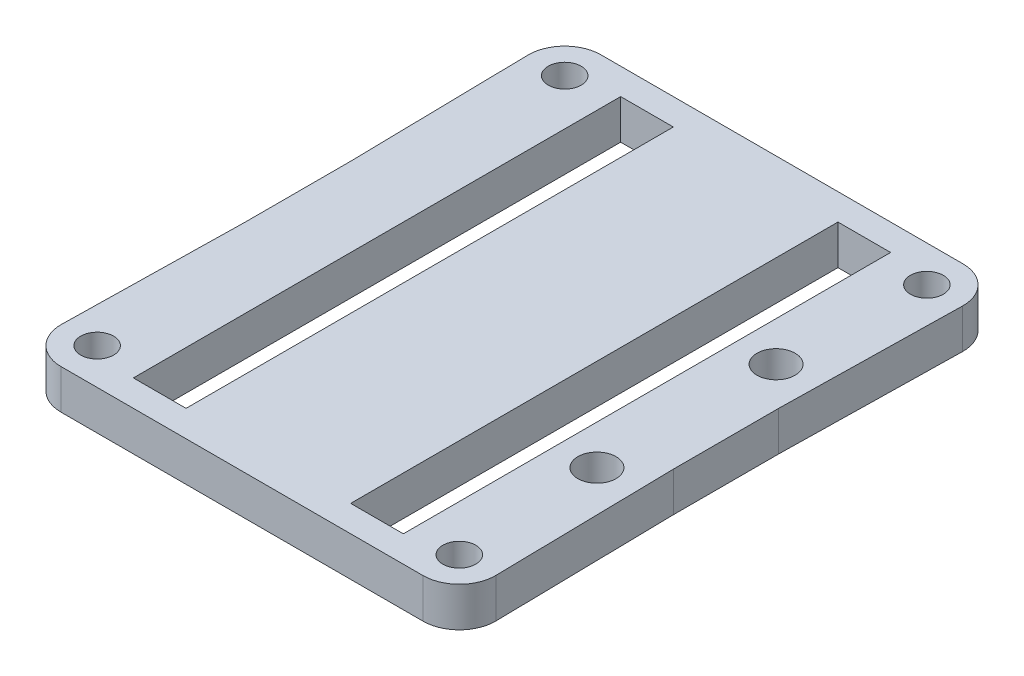
SolidWorks part; units mm, degrees
ref_plane "Front Plane" through (0, 0, 0) normal (0, 0, 1) x (1, 0, 0)
ref_plane "Top Plane" through (0, 0, 0) normal (0, 1, 0) x (1, 0, 0)
ref_plane "Right Plane" through (0, 0, 0) normal (1, 0, 0) x (0, 0, -1)
sketch "Sketch1" plane through (0, 0, 0) normal (0, 1, 0) x (1, 0, 0)
  line L5 (-6.25, 18.5) -> (6.25, 18.5)
  line L6 (-6.25, 18.5) -> (-6.25, -18.5)
  line L13 (-13.75, -17.75) -> (13.75, -17.75) construction
  line L14 (-13.75, -17.75) -> (-13.75, 17.75) construction
  line L15 (-13.75, 17.75) -> (13.75, 17.75) construction
  line L16 (13.75, -17.75) -> (13.75, 17.75) construction
  line L17 (-13.75, -17.75) -> (13.75, 17.75) construction
  line L18 (-13.75, 17.75) -> (13.75, -17.75) construction
  line L25 (-6.25, -18.5) -> (6.25, -18.5)
  line L26 (6.25, 18.5) -> (6.25, -18.5)
  line L27 (-6.25, 18.5) -> (6.25, -18.5) construction
  line L28 (-6.25, -18.5) -> (6.25, 18.5) construction
  line L29 (10.25, 18.5) -> (10.25, -18.5)
  line L30 (0, 0) -> (0, 50000) construction
  line L31 (0, 0) -> (50000, 0) construction
  line L32 (10.25, 18.5) -> (6.25, 18.5)
  line L33 (13.75, 20.5) -> (-13.75, 20.5)
  line L34 (16.25, 4) -> (16.25, 0)
  line L35 (-9, -22.0588) -> (9, -22.0588) construction
  line L36 (16.25, 4) -> (16.4995, 17.6999)
  line L37 (16.25, 18.5) -> (16.25, -18.5) construction
  line L38 (16.25, -4) -> (16.25, 0)
  line L39 (10.25, 18.5) -> (10.25, -18.5) construction
  line L40 (16.25, -4) -> (16.4995, -17.6999)
  line L41 (10.25, -18.5) -> (6.25, -18.5)
  line L42 (13.75, -20.5) -> (-13.75, -20.5)
  line L43 (-13.75, -17.75) -> (-13.75, 17.75) construction
  line L44 (-16.25, -4) -> (-16.4995, -17.6999)
  line L45 (-16.25, -4) -> (-16.25, 0)
  line L46 (-16.25, 4) -> (-16.4995, 17.6999)
  line L47 (-16.25, 4) -> (-16.25, 0)
  line L48 (-10.25, -18.5) -> (-6.25, -18.5)
  line L49 (-10.25, 18.5) -> (-10.25, -18.5)
  line L50 (-6.25, 18.5) -> (-10.25, 18.5)
  line L51 (13.25, -6.8) -> (13.25, 6.8)
  line L52 (10.25, 0) -> (16.25, 0) construction
  circle A2 centre (0, 0) radius 25 construction
  arc A3 (16.4995, 17.6999) -> (13.75, 20.5) centre (13.75, 17.75) ccw
  circle A4 centre (13.75, 17.75) radius 1.25
  circle A5 centre (13.75, -17.75) radius 1.25
  arc A6 (16.4995, -17.6999) -> (13.75, -20.5) centre (13.75, -17.75) cw
  circle A7 centre (-13.75, 17.75) radius 1.25
  arc A8 (-16.4995, 17.6999) -> (-13.75, 20.5) centre (-13.75, 17.75) cw
  arc A9 (-16.4995, -17.6999) -> (-13.75, -20.5) centre (-13.75, -17.75) ccw
  circle A10 centre (-13.75, -17.75) radius 1.25
  point P0 (0, 0)
  point P6 (0, 0)
  point P11 (0, 0)
  point P29 (0, -22.0588)
  point P38 (10.25, 0)
  point P40 (0, 20.5)
  point P47 (0, -20.5)
  point P56 (13.25, 0)
  dimension "D7" = 50
  dimension "D10" = 5.5
  dimension "D4" = 2.5
  dimension "D5" = 35.5
  dimension "D6" = 27.5
  dimension "D2" = 12.5
  dimension "D11" = 37
  dimension "D9" = 18
  dimension "D12" = 4
  dimension "D15" = 13.6
  dimension "D3" = 4
  dimension "D8" = 6
extrude "Boss-Extrude1" add sketch "Sketch1" along normal blind 3 contours L44 A9 L42 A6 L40 L38 L34 L36 A3 L33 A8 L46 L47 L45 A10 A7 L50 L5 L32 L29 L41 L25 L48 L49 A4 A5 | L26 L5 L6 L25
hole_wizard "M2.5 Clearance Hole1" positions "Sketch2" profile "Sketch3" hole size "M2.5" standard "ANSI Metric" end condition through all
sketch "Sketch2" plane through (0, 0, 0) normal (0, 1, 0) x (1, 0, 0)
  point P0 (13.25, 6.8)
  point P3 (13.25, -6.8)
sketch "Sketch3" plane through (13.25, 0, -6.8) normal (1, 0, 0) x (0, 0, -1)
  line L0 (0, 0) -> (0, 3)
  line L1 (0, 3) -> (1.45, 3)
  line L2 (1.45, 3) -> (1.45, 0)
  line L5 (1.45, 0) -> (0, 0)
  line L11 (0, -6.35) -> (0, 107.95) construction
  dimension "Thru Hole Dia." = 2.9
  dimension "Thru Hole Depth" = 3
equation "\"D15@Sketch1\"=19-(2.7*2)"
